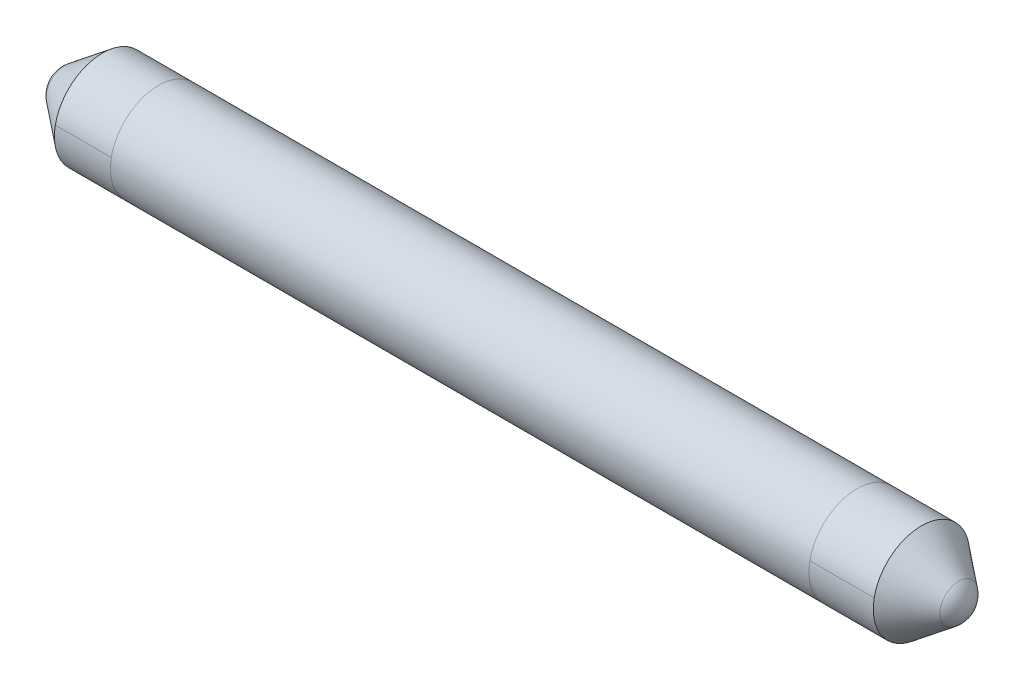
SolidWorks part; units mm, degrees
ref_plane "Plane1" through (0, 0, 0) normal (0, 0, 1) x (1, 0, 0)
ref_plane "Plane2" through (0, 0, 0) normal (0, 1, 0) x (1, 0, 0)
ref_plane "Plane3" through (0, 0, 0) normal (1, 0, 0) x (0, 0, -1)
other "Configuration Table"
sketch "Sketch1" plane through (0, 0, 0) normal (0, 0, 1) x (1, 0, 0)
  line L0 (0, -101.644) -> (-189.3727, -101.644)
  line L2 (-100, -81.644) -> (0, -81.644)
  line L3 (0, -81.644) -> (0, -101.644)
  line L4 (-160, -81.644) -> (-100, -81.644)
  line L5 (-170, -81.644) -> (-160, -81.644)
  line L7 (-170, -81.644) -> (-185.5252, -93.7607)
  line L8 (0, -101.644) -> (-189.3727, -101.644) construction
  arc A0 (-189.3727, -101.644) -> (-185.5252, -93.7607) centre (-179.3727, -101.644) cw
  dimension "D1" = 10
revolve "Base-Revolve" add sketch "Sketch1" angle 360 about L8
mirror "Mirror1" about plane through (0, 0, 0) normal (1, 0, 0) of "Base-Revolve"
sketch "Sketch2" plane through (0, 0, 0) normal (0, 0, 1) x (1, 0, 0)
  line L2 (-146.7494, -181.4119) -> (-146.7494, -61.9651)
split line "Split Line6"
sketch "Sketch15" plane through (0, 0, 0) normal (0, 0, 1) x (1, 0, 0)
  line L1 (143.2847, -65.1497) -> (143.2847, -144.6165)
split line "Split Line26"
split line "Split Line29"
sketch "Sketch2" plane through (0, -56.3041, 0) normal (0, 0, -1) x (-1, 0, 0)
  line L0 (-233.0538, -41.4662) -> (212.4902, -41.4662)
